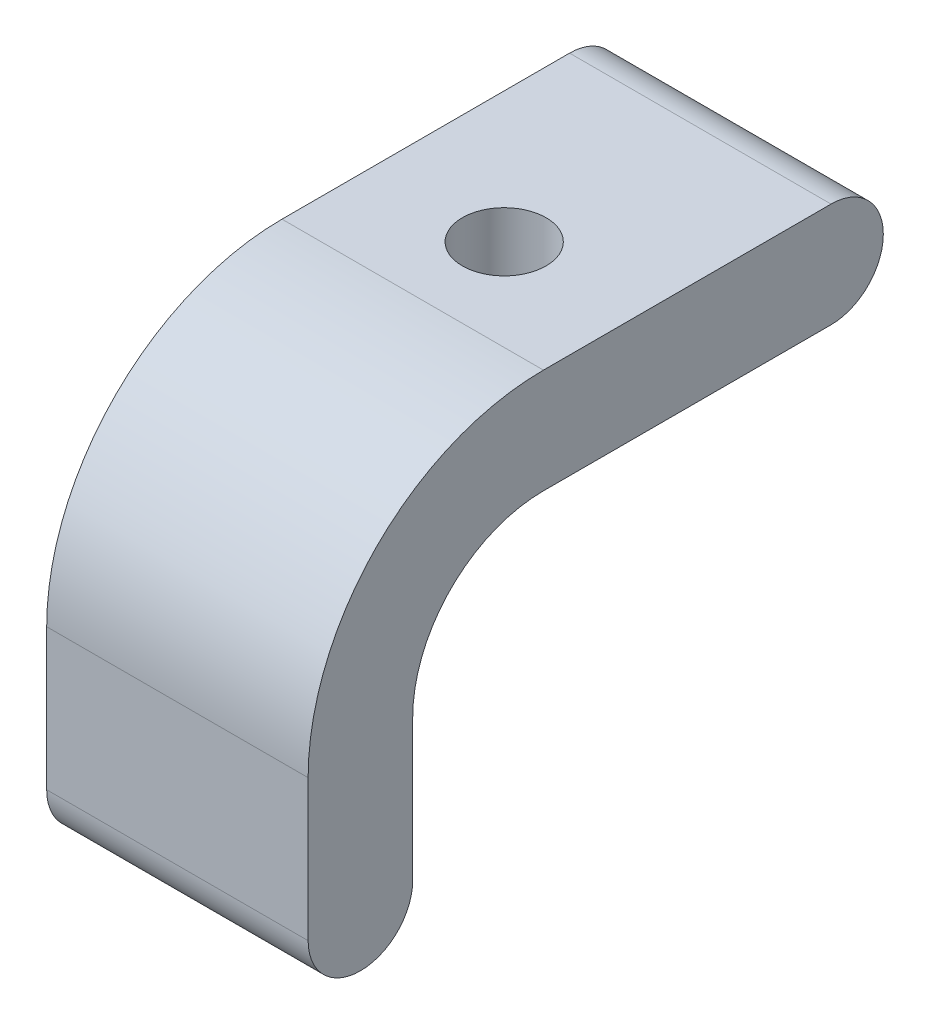
SolidWorks part; units mm, degrees
material "5082 Al"
ref_plane "Front" through (0, 0, 0) normal (0, 0, 1) x (1, 0, 0)
ref_plane "Top" through (0, 0, 0) normal (0, 1, 0) x (1, 0, 0)
ref_plane "Right" through (0, 0, 0) normal (1, 0, 0) x (0, 0, -1)
sketch "Sketch1" plane through (0, 0, 0) normal (1, 0, 0) x (0, 0, -1)
  line L0 (0, 0) -> (11, 0)
  line L1 (11, 4) -> (0, 4)
  line L2 (-5, -5) -> (-5, -10.4)
  line L3 (-9, -5) -> (-9, -10.4)
  arc A0 (11, 4) -> (11, 0) centre (11, 2) cw
  arc A1 (0, 0) -> (-5, -5) centre (0, -5) ccw
  arc A2 (-5, -10.4) -> (-9, -10.4) centre (-7, -10.4) cw
  arc A3 (-9, -5) -> (0, 4) centre (0, -5) cw
  dimension "D1" = 2
  dimension "D2" = 2
  dimension "D3" = 5
  dimension "D4" = 10.4
  dimension "D5" = 20
extrude "Boss-Extrude1" add sketch "Sketch1" along normal blind 10
ref_plane "Plane1" through (5, 0, 0) normal (1, 0, 0) x (0, 0, -1)
sketch "Sketch2" plane through (0, 4, 0) normal (0, 1, 0) x (1, 0, 0)
  line L0 (5, -7.92) -> (5, 7.92) construction
  line L1 (10, 13) -> (0, 13) construction
  circle A0 centre (5, 3.5) radius 1.6
  dimension "D2" = 3.2
  dimension "D1" = 9.5
extrude "Cut-Extrude1" cut sketch "Sketch2" against normal blind 10
